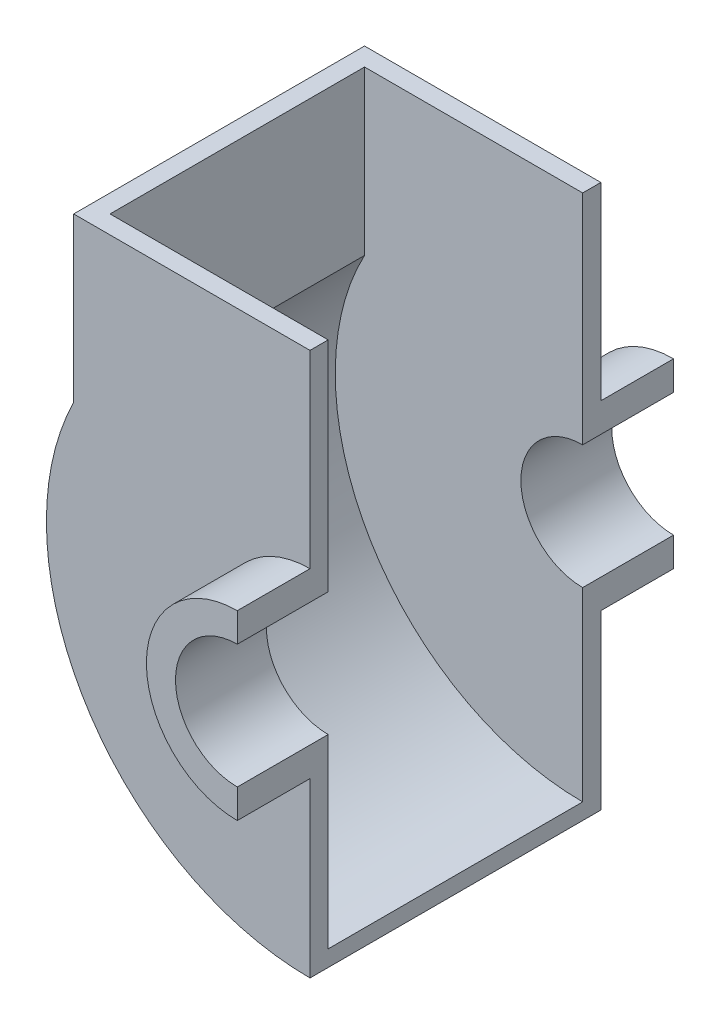
SolidWorks part; units mm, degrees
ref_plane "Front Plane" through (0, 0, 0) normal (0, 0, 1) x (1, 0, 0)
ref_plane "Top Plane" through (0, 0, 0) normal (0, 1, 0) x (1, 0, 0)
ref_plane "Right Plane" through (0, 0, 0) normal (1, 0, 0) x (0, 0, -1)
sketch "Sketch1" plane through (0, 0, 0) normal (0, 0, 1) x (1, 0, 0)
  line L0 (0, 25) -> (0, 17)
  line L1 (0, -17) -> (0, -25)
  arc A0 (0, 25) -> (0, -25) centre (0, 0) ccw
  arc A1 (0, 17) -> (0, -17) centre (0, 0) ccw
  dimension "D1" = 50
  dimension "D2" = 34
extrude "Boss-Extrude1" add sketch "Sketch1" along normal blind 20 and the other way blind 5
sketch "Sketch2" plane through (0, 0, 0) normal (0, 0, 1) x (1, 0, 0)
  line L0 (0, -25) -> (0, -72.5)
  line L1 (0, 25) -> (0, 77)
  line L2 (0, 77) -> (-65, 77)
  line L3 (-65, 77) -> (-65, 32.1131)
  arc A1 (-65, 32.1131) -> (0, -72.5) centre (0, 0) ccw
  arc A2 (0, -25) -> (0, 25) centre (0, 0) cw
  arc A3 (0, 25) -> (0, -25) centre (0, 0) ccw construction
  dimension "D1" = 145
  dimension "D4" = 25
  dimension "D2" = 52
  dimension "D3" = 65
extrude "Boss-Extrude4" add sketch "Sketch2" against normal blind 5
ref_plane "Plane1" through (0, 0, -40) normal (0, 0, 1) x (1, 0, 0)
mirror "Mirror1" about plane through (0, 0, -40) normal (0, 0, 1) of "Boss-Extrude4", "Boss-Extrude1"
mirror "Mirror2" about plane through (0, 0, -40) normal (0, 0, 1)
sketch "Sketch3" plane through (0, 0, 0) normal (0, 0, 1) x (1, 0, 0)
  line L0 (-65, 32.1131) -> (-65, 77)
  line L1 (-65, 77) -> (-60, 77)
  line L2 (0, 77) -> (-65, 77) construction
  line L3 (-60, 77) -> (-60, 32.1131)
  line L4 (0, -68.0533) -> (0, -72.5)
  arc A0 (-65, 32.1131) -> (0, -72.5) centre (0, 0) ccw
  arc A2 (-60, 32.1131) -> (0, -68.0533) centre (0, 0) ccw
  dimension "D1" = 145
  dimension "D2" = 5
extrude "Boss-Extrude5" add sketch "Sketch3" against normal up to body (80 mm away) separate body
